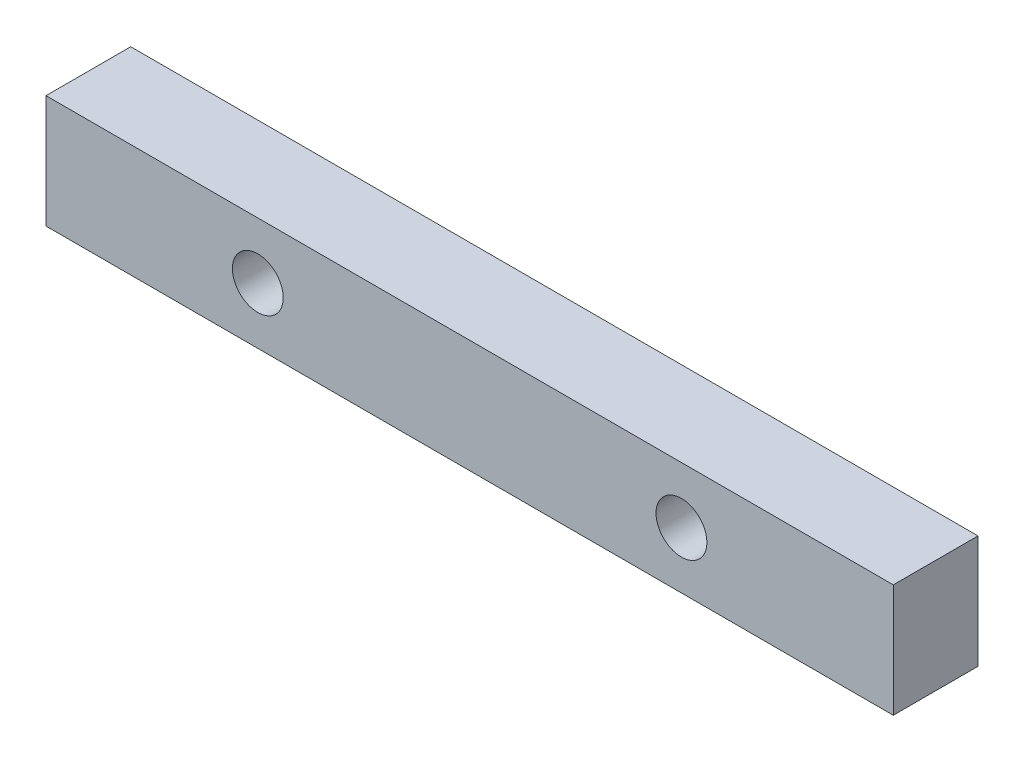
SolidWorks part; units mm, degrees
ref_plane "Front Plane" through (0, 0, 0) normal (0, 0, 1) x (1, 0, 0)
ref_plane "Top Plane" through (0, 0, 0) normal (0, 1, 0) x (1, 0, 0)
ref_plane "Right Plane" through (0, 0, 0) normal (1, 0, 0) x (0, 0, -1)
sketch "Sketch1" plane through (0, 0, 0) normal (0, 0, 1) x (1, 0, 0)
  line L0 (-75, 0) -> (75, 0) construction
  line L1 (-75, -10) -> (75, -10)
  line L2 (-75, -10) -> (-75, 10)
  line L3 (-75, 10) -> (75, 10)
  line L4 (75, -10) -> (75, 10)
  line L5 (-75, -10) -> (75, 10) construction
  line L6 (-75, 10) -> (75, -10) construction
  point P0 (0, 0)
  point P8 (-37.5, 0)
  point P9 (37.5, 0)
  dimension "D1" = 150
  dimension "D2" = 20
  dimension "D3" = 37.5
  dimension "D4" = 37.5
extrude "Boss-Extrude1" add sketch "Sketch1" along normal blind 15
hole_wizard "CSK for M8 SFHCS1" positions "Sketch5" profile "Sketch4" countersink size "M8" standard "ANSI Metric" end condition through all
sketch "Sketch5" plane through (0, 0, 0) normal (0, 0, -1) x (-1, 0, 0)
  point P0 (-37.5, 0)
  point P3 (37.5, 0)
sketch "Sketch4" plane through (37.5, 0, 0) normal (1, 0, 0) x (0, 1, 0)
  line L0 (0, 0) -> (0, 15)
  line L1 (0, 15) -> (4.5, 15)
  line L2 (4.5, 15) -> (4.5, 4.46)
  line L3 (4.5, 4.46) -> (8.96, 0)
  line L5 (8.96, 0) -> (0, 0)
  line L6 (-4.5, 4.46) -> (-8.96, 0) construction
  line L11 (0, -6.35) -> (0, 107.95) construction
  dimension "Thru Hole Dia." = 9
  dimension "Thru Hole Depth" = 15
  dimension "Near C'Sink Dia." = 17.92
  dimension "Near C'Sink Angle" = 90
